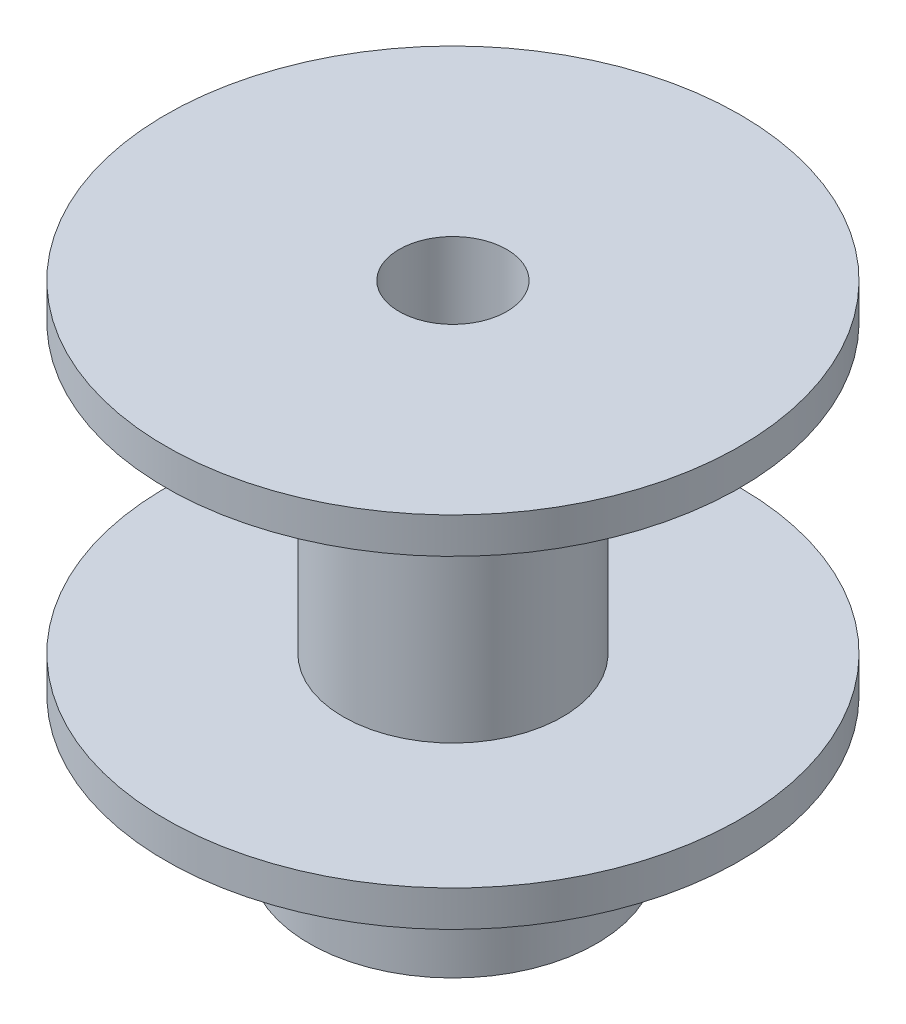
SolidWorks part; units mm, degrees
ref_plane "Front Plane" through (0, 0, 0) normal (0, 0, 1) x (1, 0, 0)
ref_plane "Top Plane" through (0, 0, 0) normal (0, 1, 0) x (1, 0, 0)
ref_plane "Right Plane" through (0, 0, 0) normal (1, 0, 0) x (0, 0, -1)
sketch "Sketch1" plane through (0, 0, 0) normal (0, 0, 1) x (1, 0, 0)
  line L0 (-2.3813, 15.875) -> (-12.7, 15.875)
  line L1 (-12.7, 15.875) -> (-12.7, 14.2875)
  line L2 (-12.7, 14.2875) -> (-4.8514, 14.2875)
  line L3 (-4.8514, 14.2875) -> (-4.8514, 1.5875)
  line L4 (-4.8514, 1.5875) -> (-12.7, 1.5875)
  line L5 (-12.7, 1.5875) -> (-12.7, 0)
  line L6 (-12.7, 0) -> (-6.35, 0)
  line L7 (-6.35, 0) -> (-6.35, -6.35)
  line L8 (-6.35, -6.35) -> (-2.3812, -6.35)
  line L9 (-2.3812, -6.35) -> (-2.3813, 15.875)
  line L10 (0, -8.9764) -> (0, 15.3246) construction
  dimension "D1" = 2.3813
  dimension "D2" = 12.7
  dimension "D3" = 15.875
  dimension "D4" = 6.35
  dimension "D5" = 22.225
  dimension "D6" = 9.7028
  dimension "D7" = 12.7
revolve "Revolve1" add sketch "Sketch1" angle 360 about L10
